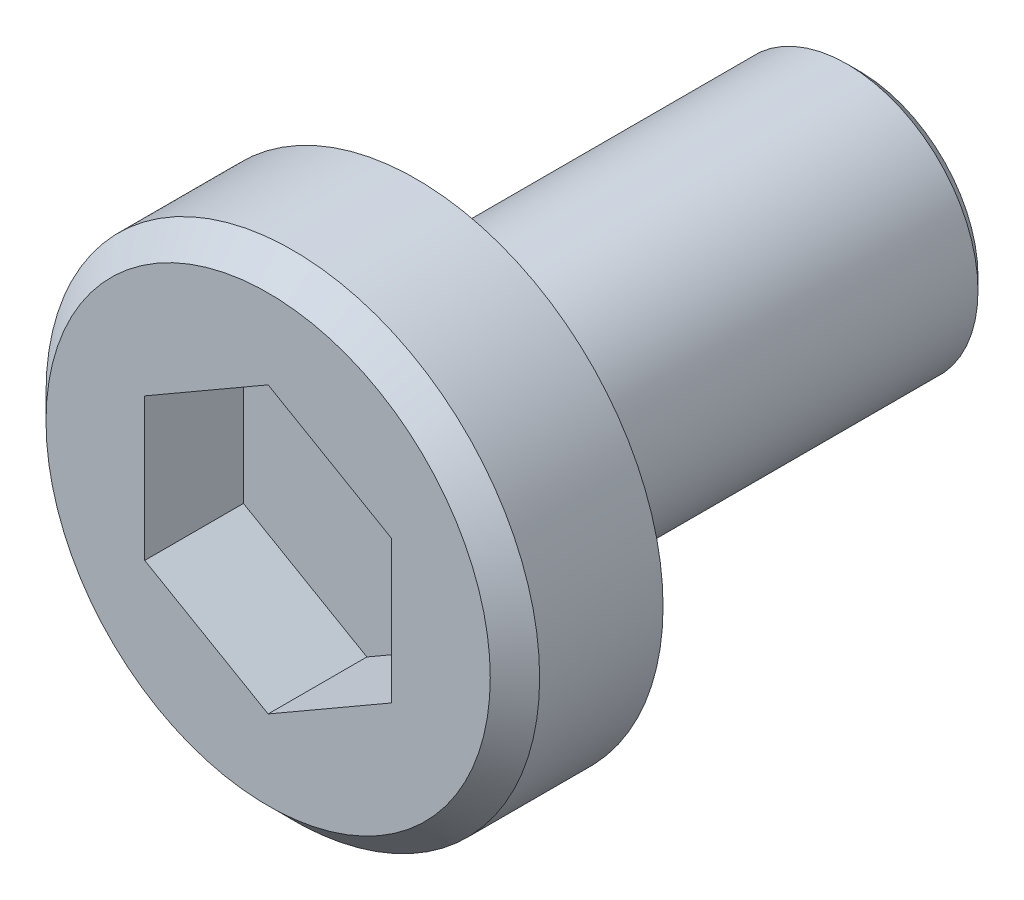
SolidWorks part; units mm, degrees
ref_plane "Front Plane" through (0, 0, 0) normal (0, 0, 1) x (1, 0, 0)
ref_plane "Top Plane" through (0, 0, 0) normal (0, 1, 0) x (1, 0, 0)
ref_plane "Right Plane" through (0, 0, 0) normal (1, 0, 0) x (0, 0, -1)
sketch "Sketch1" plane through (0, 0, 0) normal (1, 0, 0) x (0, 0, -1)
  line L0 (0, 0) -> (243.0266, 0) construction
  line L1 (0, 0) -> (0, 5)
  line L2 (0, 5) -> (3, 5)
  line L3 (3, 5) -> (3, 2.65)
  line L4 (3, 2.65) -> (11.98, 2.65)
  line L5 (11.98, 2.65) -> (11.98, 0)
  line L6 (11.98, 0) -> (0, 0)
  dimension "D1" = 11.98
  dimension "D2" = 5.3
  dimension "D3" = 10
  dimension "D4" = 3
revolve "Revolve1" add sketch "Sketch1" angle 360 about L0
sketch "Sketch2" plane through (0, 0, 0) normal (0, 0, 1) x (1, 0, 0)
  line L1 (0, 2.8868) -> (-2.5, 1.4434)
  line L2 (-2.5, 1.4434) -> (-2.5, -1.4434)
  line L3 (-2.5, -1.4434) -> (0, -2.8868)
  line L4 (0, -2.8868) -> (2.5, -1.4434)
  line L5 (2.5, -1.4434) -> (2.5, 1.4434)
  line L6 (2.5, 1.4434) -> (0, 2.8868)
  circle A0 centre (0, 0) radius 2.5 construction
  dimension "D1" = 5
extrude "Cut-Extrude2" cut sketch "Sketch2" against normal blind 2
chamfer "Chamfer1" distance 0.5 angle 45 1 edges at (5, 0, 0)
chamfer "Chamfer2" distance 0.25 angle 45 1 edges at (2.65, 0, -11.98)
